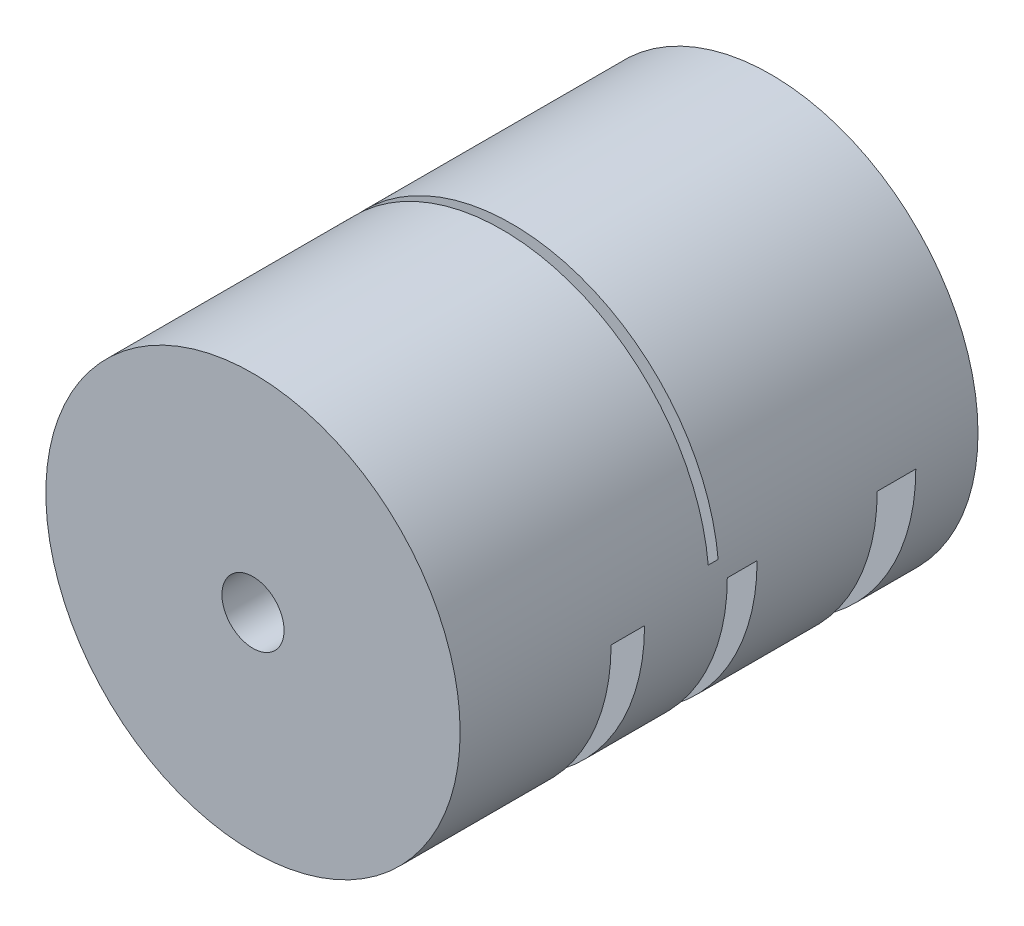
SolidWorks part; units mm, degrees
ref_plane "Front Plane" through (0, 0, 0) normal (0, 0, 1) x (1, 0, 0)
ref_plane "Top Plane" through (0, 0, 0) normal (0, 1, 0) x (1, 0, 0)
ref_plane "Right Plane" through (0, 0, 0) normal (1, 0, 0) x (0, 0, -1)
sketch "Sketch1" plane through (0, 0, 0) normal (0, 0, 1) x (1, 0, 0)
  circle A0 centre (0, 0) radius 20
extrude "Boss-Extrude1" add sketch "Sketch1" along normal mid plane 50
sketch "Sketch2" plane through (0, 0, 0) normal (0, 1, 0) x (1, 0, 0)
  line L1 (-22.059, 18.9939) -> (23.2953, 18.9939)
  line L2 (-22.059, 18.9939) -> (-22.059, 15.2692)
  line L3 (-22.059, 15.2692) -> (23.2953, 15.2692)
  line L4 (23.2953, 18.9939) -> (23.2953, 15.2692)
  line L5 (-22.059, 3.6714) -> (23.2953, 3.6714)
  line L6 (-22.059, 3.6714) -> (-22.059, 0.794)
  line L7 (-22.059, 0.794) -> (23.2953, 0.794)
  line L8 (23.2953, 3.6714) -> (23.2953, 0.794)
  line L9 (23.2953, -10.4261) -> (-22.059, -10.4261)
  line L10 (23.2953, -10.4261) -> (23.2953, -7.1961)
  line L11 (23.2953, -7.1961) -> (-22.059, -7.1961)
  line L12 (-22.059, -10.4261) -> (-22.059, -7.1961)
extrude "Cut-Extrude1" cut sketch "Sketch2" against normal up to next
sketch "Sketch3" plane through (0, 0, 0) normal (0, 1, 0) x (1, 0, 0)
  line L0 (-20, 0.794) -> (-20, -7.1961) construction
  line L1 (-20, 0) -> (19.9098, 0)
  line L2 (-20, 0) -> (-20, -0.9541)
  line L3 (-20, -0.9541) -> (19.9098, -0.9541)
  line L4 (19.9098, 0) -> (19.9098, -0.9541)
extrude "Cut-Extrude2" cut sketch "Sketch3" along normal up to next
sketch "Sketch4" plane through (0, 0, -25) normal (0, 0, -1) x (-1, 0, 0)
  circle A0 centre (0, 0) radius 3
extrude "Cut-Extrude3" cut sketch "Sketch4" against normal through all
sketch "Sketch5" plane through (0, 0, -25) normal (0, 0, -1) x (-1, 0, 0)
  circle A0 centre (0, 0) radius 4
  dimension "D1" = 8
extrude "Cut-Extrude4" cut sketch "Sketch5" against normal blind 10
